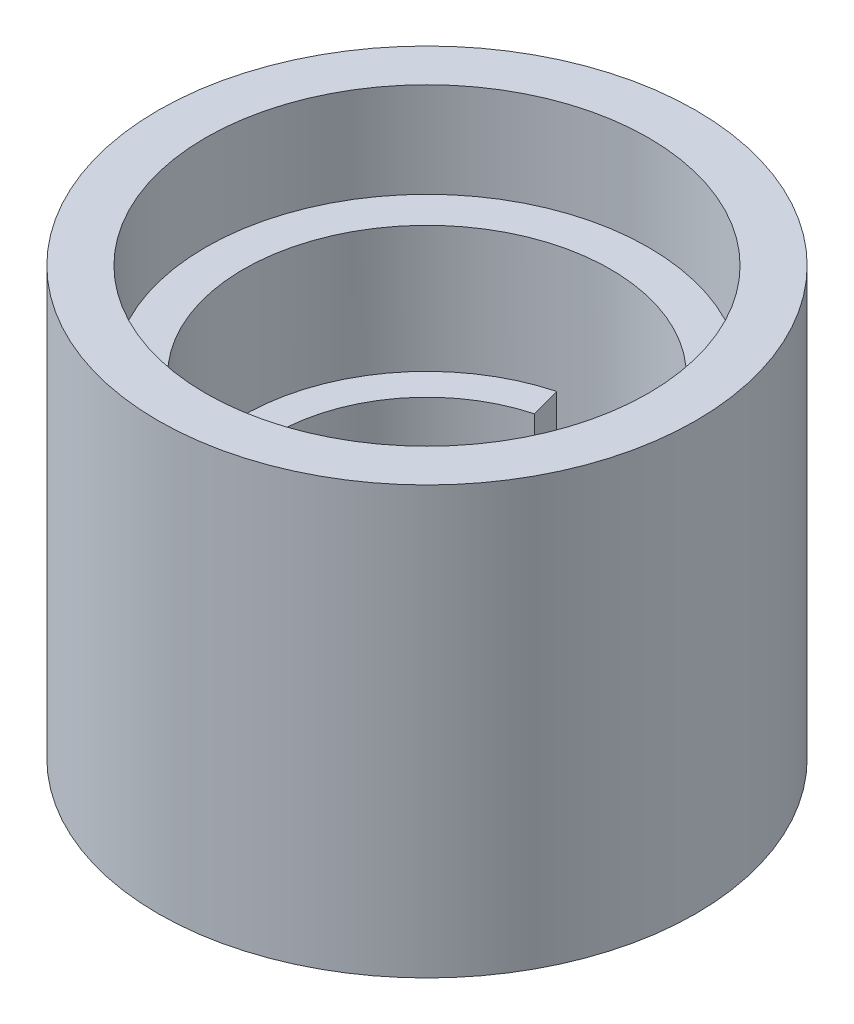
SolidWorks part; units mm, degrees
ref_plane "Front Plane" through (0, 0, 0) normal (0, 0, 1) x (1, 0, 0)
ref_plane "Top Plane" through (0, 0, 0) normal (0, 1, 0) x (1, 0, 0)
ref_plane "Right Plane" through (0, 0, 0) normal (1, 0, 0) x (0, 0, -1)
sketch "Sketch1" plane through (0, 0, 0) normal (0, 1, 0) x (1, 0, 0)
  circle A1 centre (0, 0) radius 10.795
  circle A2 centre (0, 0) radius 6.096
  dimension "D1" = 21.59
  dimension "D2" = 12.192
extrude "Boss-Extrude1" add sketch "Sketch1" along normal blind 17.145 contours A1 A2
sketch "Sketch2" plane through (0, 17.145, 0) normal (0, 1, 0) x (1, 0, 0)
  circle A0 centre (0, 0) radius 8.89
  circle A2 centre (0, 0) radius 6.096 construction
  dimension "D1" = 17.78
extrude "Cut-Extrude1" cut sketch "Sketch2" against normal blind 3.81
sketch "Sketch3" plane through (0, 13.335, 0) normal (0, 1, 0) x (1, 0, 0)
  circle A0 centre (0, 0) radius 6.096
  circle A1 centre (0, 0) radius 6.096 construction
  circle A2 centre (0, 0) radius 7.366
  dimension "D1" = 1.27
extrude "Cut-Extrude2" cut sketch "Sketch3" against normal blind 5.08
sketch "Sketch4" plane through (0, 8.255, 0) normal (0, 1, 0) x (1, 0, 0)
  line L0 (0, 0) -> (-1.9065, 7.115)
  line L1 (0, 0) -> (0, 7.366) construction
  line L2 (0, 0) -> (1.9065, 7.115)
  circle A0 centre (0, 0) radius 7.366 construction
  arc A1 (1.9065, 7.115) -> (-1.9065, 7.115) centre (0, 0) ccw
  dimension "D1" = 15
  dimension "D2" = 15
extrude "Cut-Extrude3" cut sketch "Sketch4" against normal up to surface (8.255 mm away) up to face at (0, 0, 6.096)
